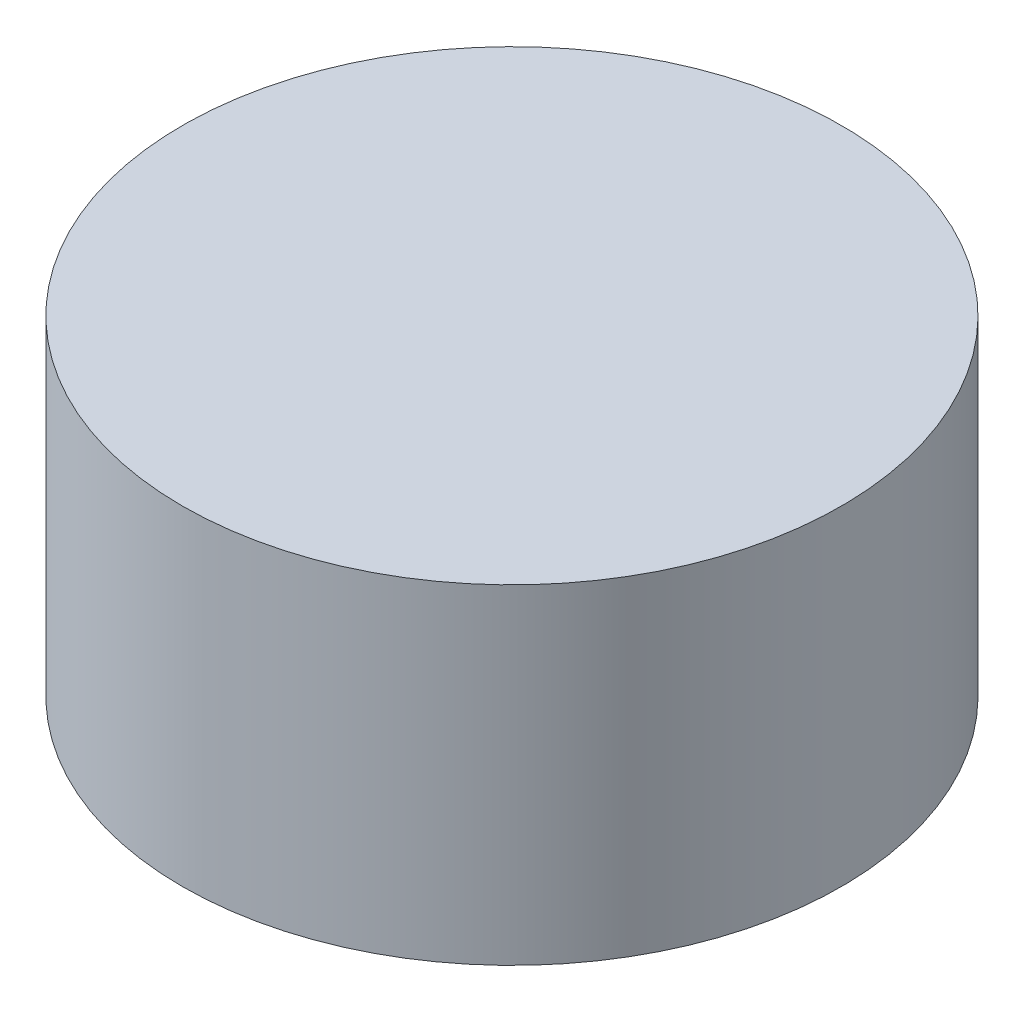
SolidWorks part; units mm, degrees
material "AISI 4130 Steel, normalized at 870C"
ref_plane "Front Plane" through (0, 0, 0) normal (0, 0, 1) x (1, 0, 0)
ref_plane "Top Plane" through (0, 0, 0) normal (0, 1, 0) x (1, 0, 0)
ref_plane "Right Plane" through (0, 0, 0) normal (1, 0, 0) x (0, 0, -1)
sketch "Sketch1" plane through (0, 0, 0) normal (0, 1, 0) x (1, 0, 0)
  circle A0 centre (0, 0) radius 20
  dimension "D1" = 40
extrude "Boss-Extrude1" add sketch "Sketch1" along normal blind 20 contours A0
